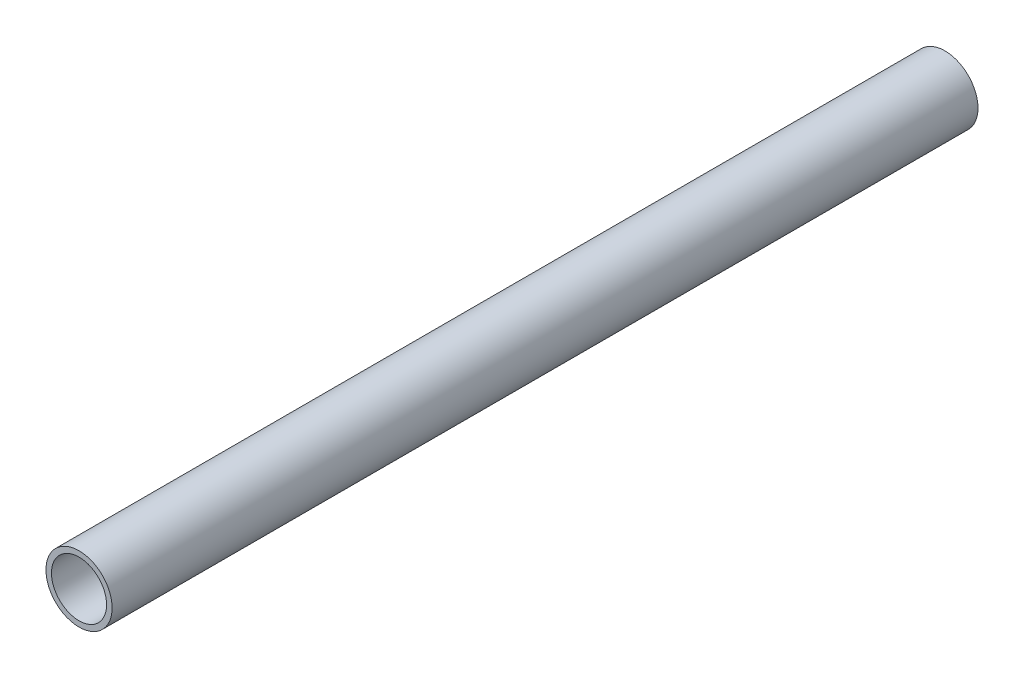
SolidWorks part; units mm, degrees
ref_plane "Ön Düzlem" through (0, 0, 0) normal (0, 0, 1) x (1, 0, 0)
ref_plane "Üst Düzlem" through (0, 0, 0) normal (0, 1, 0) x (1, 0, 0)
ref_plane "Sağ Düzlem" through (0, 0, 0) normal (1, 0, 0) x (0, 0, -1)
sketch "Sketch1" plane through (0, 0, 0) normal (0, 0, 1) x (1, 0, 0)
  circle A0 centre (0, 0) radius 6
  circle A1 centre (0, 0) radius 5
  dimension "D1" = 10
  dimension "D2" = 1
extrude "Boss-Extrude1" add sketch "Sketch1" along normal blind 157
